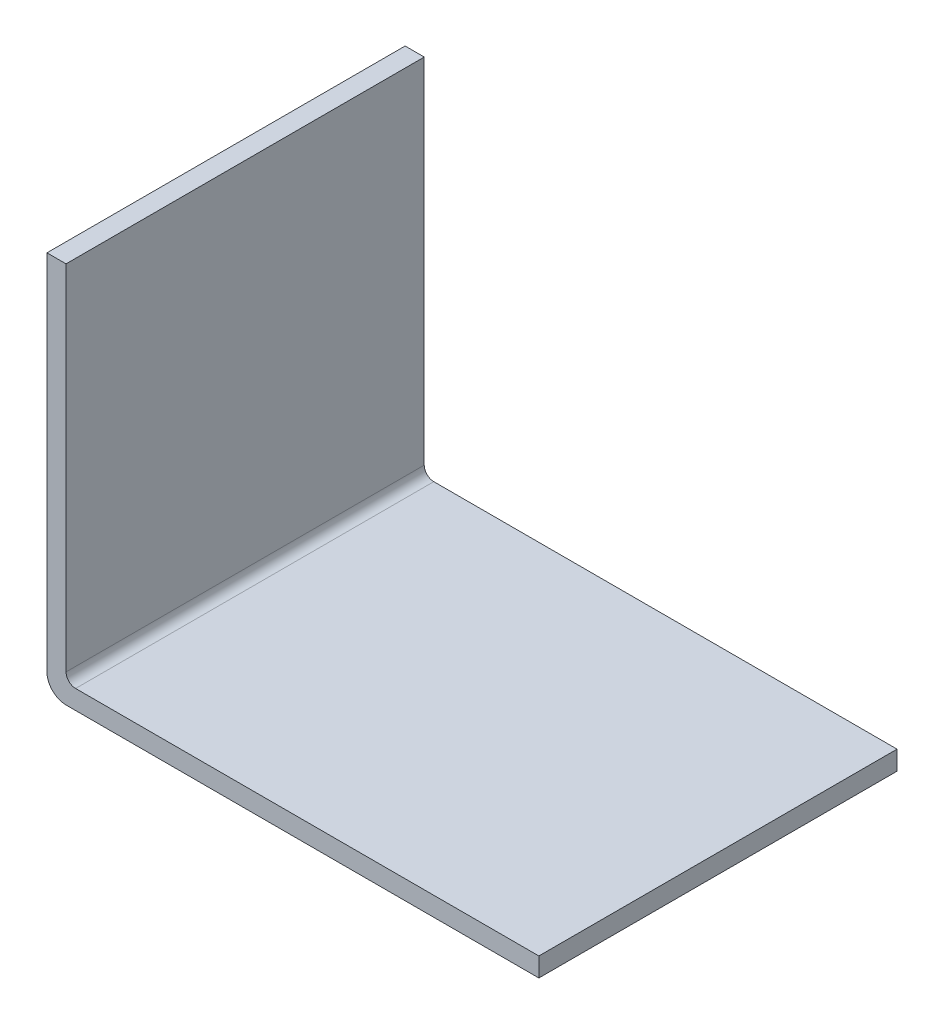
SolidWorks part; units mm, degrees
ref_plane "Front Plane" through (0, 0, 0) normal (0, 0, 1) x (1, 0, 0)
ref_plane "Top Plane" through (0, 0, 0) normal (0, 1, 0) x (1, 0, 0)
ref_plane "Right Plane" through (0, 0, 0) normal (1, 0, 0) x (0, 0, -1)
sketch "Sketch1" plane through (0, 0, 0) normal (0, 1, 0) x (1, 0, 0)
  line L1 (-25.75, -18.75) -> (25.75, -18.75)
  line L2 (-25.75, -18.75) -> (-25.75, 18.75)
  line L3 (-25.75, 18.75) -> (25.75, 18.75)
  line L4 (25.75, -18.75) -> (25.75, 18.75)
  line L5 (-25.75, -18.75) -> (25.75, 18.75) construction
  line L6 (-25.75, 18.75) -> (25.75, -18.75) construction
  point P0 (0, 0)
  dimension "D1" = 37.5
  dimension "D2" = 51.5
extrude "Boss-Extrude1" add sketch "Sketch1" along normal blind 40
sketch "Sketch2" plane through (0, 0, 18.75) normal (0, 0, 1) x (1, 0, 0)
  line L0 (-25.75, 0) -> (25.75, 0) construction
  line L1 (-23.75, 2) -> (25.75, 2)
  line L2 (-23.75, 2) -> (-23.75, 40)
  line L3 (-23.75, 40) -> (25.75, 40)
  line L4 (25.75, 2) -> (25.75, 40)
  line L5 (-25.75, 40) -> (-25.75, 0) construction
  dimension "D1" = 2
  dimension "D2" = 2
extrude "Cut-Extrude1" cut sketch "Sketch2" against normal through all
fillet "Fillet1" radius 1 1 edges at (-23.75, 2, 0)
fillet "Fillet2" radius 2 1 edges at (-25.75, 0, 0)
sketch "Sketch3" plane through (0, 2, 0) normal (0, 1, 0) x (1, 0, 0)
  line L1 (-14.9413, -15.575) -> (-14.9413, 15.575) construction
  point P2 (-14.9413, 0)
  dimension "D1" = 31.15
